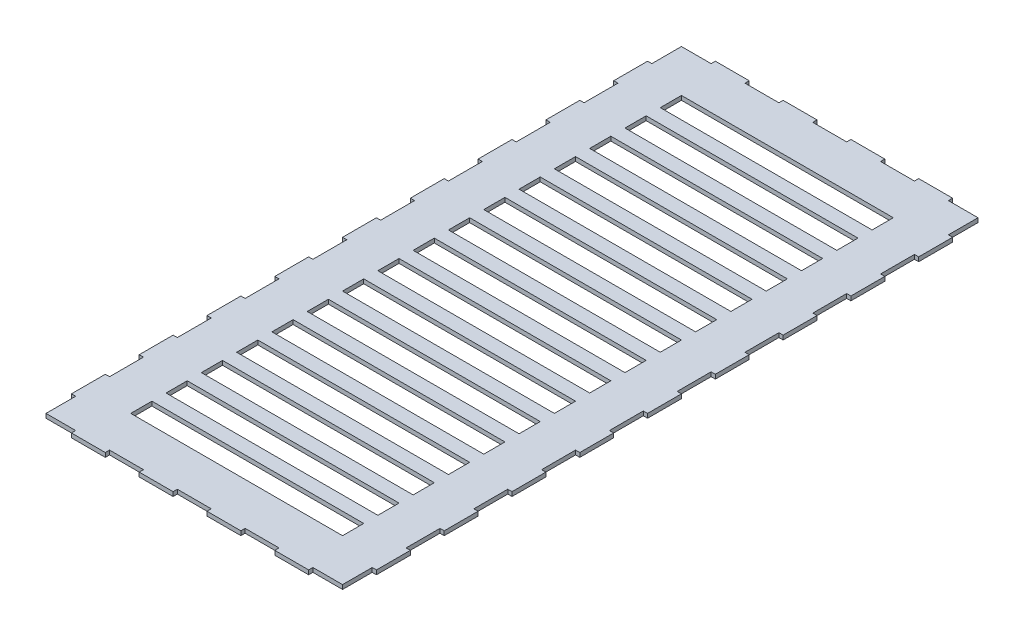
SolidWorks part; units mm, degrees
ref_plane "Front Plane" through (0, 0, 0) normal (0, 0, 1) x (1, 0, 0)
ref_plane "Top Plane" through (0, 0, 0) normal (0, 1, 0) x (1, 0, 0)
ref_plane "Right Plane" through (0, 0, 0) normal (1, 0, 0) x (0, 0, -1)
sketch "Sketch1" plane through (0, 0, 0) normal (0, 1, 0) x (1, 0, 0)
  line L0 (-75, -170) -> (-75, -155)
  line L1 (-105, -225) -> (105, -225)
  line L2 (-105, -225) -> (-105, 225)
  line L3 (-105, 225) -> (105, 225)
  line L4 (105, -225) -> (105, 225)
  line L5 (-105, -225) -> (105, 225) construction
  line L6 (-105, 225) -> (105, -225) construction
  line L7 (-75, -195) -> (75, -195)
  line L8 (-75, -195) -> (-75, -180)
  line L9 (-75, -180) -> (75, -180)
  line L10 (75, -195) -> (75, -180)
  line L11 (-75, -170) -> (75, -170)
  line L12 (75, -170) -> (75, -155)
  line L13 (-75, -155) -> (75, -155)
  line L14 (-75, -145) -> (-75, -130)
  line L15 (-75, -145) -> (75, -145)
  line L16 (75, -145) -> (75, -130)
  line L17 (-75, -130) -> (75, -130)
  line L18 (-75, -120) -> (-75, -105)
  line L19 (-75, -120) -> (75, -120)
  line L20 (75, -120) -> (75, -105)
  line L21 (-75, -105) -> (75, -105)
  line L22 (-75, -95) -> (-75, -80)
  line L23 (-75, -95) -> (75, -95)
  line L24 (75, -95) -> (75, -80)
  line L25 (-75, -80) -> (75, -80)
  line L26 (-75, -70) -> (-75, -55)
  line L27 (-75, -70) -> (75, -70)
  line L28 (75, -70) -> (75, -55)
  line L29 (-75, -55) -> (75, -55)
  line L30 (-75, -45) -> (-75, -30)
  line L31 (-75, -45) -> (75, -45)
  line L32 (75, -45) -> (75, -30)
  line L33 (-75, -30) -> (75, -30)
  line L34 (-75, -20) -> (-75, -5)
  line L35 (-75, -20) -> (75, -20)
  line L36 (75, -20) -> (75, -5)
  line L37 (-75, -5) -> (75, -5)
  line L38 (-75, 5) -> (-75, 20)
  line L39 (-75, 5) -> (75, 5)
  line L40 (75, 5) -> (75, 20)
  line L41 (-75, 20) -> (75, 20)
  line L42 (-75, 30) -> (-75, 45)
  line L43 (-75, 30) -> (75, 30)
  line L44 (75, 30) -> (75, 45)
  line L45 (-75, 45) -> (75, 45)
  line L46 (-75, 55) -> (-75, 70)
  line L47 (-75, 55) -> (75, 55)
  line L48 (75, 55) -> (75, 70)
  line L49 (-75, 70) -> (75, 70)
  line L50 (-75, 80) -> (-75, 95)
  line L51 (-75, 80) -> (75, 80)
  line L52 (75, 80) -> (75, 95)
  line L53 (-75, 95) -> (75, 95)
  line L54 (-75, 105) -> (-75, 120)
  line L55 (-75, 105) -> (75, 105)
  line L56 (75, 105) -> (75, 120)
  line L57 (-75, 120) -> (75, 120)
  line L58 (-75, 130) -> (-75, 145)
  line L59 (-75, 130) -> (75, 130)
  line L60 (75, 130) -> (75, 145)
  line L61 (-75, 145) -> (75, 145)
  line L62 (-75, 155) -> (-75, 170)
  line L63 (-75, 155) -> (75, 155)
  line L64 (75, 155) -> (75, 170)
  line L65 (-75, 170) -> (75, 170)
  line L66 (-75, 180) -> (-75, 195)
  line L67 (-75, 180) -> (75, 180)
  line L68 (75, 180) -> (75, 195)
  line L69 (-75, 195) -> (75, 195)
  point P0 (0, 0)
  dimension "D1" = 30
  dimension "D2" = 30
  dimension "D3" = 30
  dimension "D4" = 15
  dimension "D5" = 150
  dimension "D7" = 30
  dimension "D8" = 10
  dimension "D6" = 16
extrude "Boss-Extrude1" add sketch "Sketch1" along normal blind 3
sketch "Sketch2" plane through (0, 3, 0) normal (0, 1, 0) x (1, 0, 0)
  line L0 (105, 225) -> (-105, 225) construction
  line L1 (-84, 225) -> (-60, 225)
  line L2 (-84, 225) -> (-84, 228)
  line L3 (-84, 228) -> (-60, 228)
  line L4 (-60, 225) -> (-60, 228)
  line L5 (-36, 225) -> (-36, 228)
  line L6 (-36, 225) -> (-12, 225)
  line L7 (-12, 225) -> (-12, 228)
  line L8 (-36, 228) -> (-12, 228)
  line L9 (12, 225) -> (12, 228)
  line L10 (12, 225) -> (36, 225)
  line L11 (36, 225) -> (36, 228)
  line L12 (12, 228) -> (36, 228)
  line L13 (60, 225) -> (60, 228)
  line L14 (60, 225) -> (84, 225)
  line L15 (84, 225) -> (84, 228)
  line L16 (60, 228) -> (84, 228)
  line L17 (-36, -228) -> (-36, -225)
  line L18 (-36, -228) -> (-12, -228)
  line L19 (-12, -228) -> (-12, -225)
  line L20 (-36, -225) -> (-12, -225)
  line L21 (12, -228) -> (12, -225)
  line L22 (12, -228) -> (36, -228)
  line L23 (36, -228) -> (36, -225)
  line L24 (12, -225) -> (36, -225)
  line L25 (60, -228) -> (60, -225)
  line L26 (60, -228) -> (84, -228)
  line L27 (84, -228) -> (84, -225)
  line L28 (60, -225) -> (84, -225)
  line L29 (-84, -228) -> (-84, -225)
  line L30 (-84, -228) -> (-60, -228)
  line L31 (-60, -228) -> (-60, -225)
  line L32 (-84, -225) -> (-60, -225)
  line L33 (-84, 225) -> (-84, -228) construction
  line L34 (-12, 225) -> (12, 225)
  line L35 (-12, -225) -> (12, -225)
  line L38 (105, -225) -> (105, 225) construction
  point P6 (0, 225)
  point P7 (-72, 225)
  point P8 (0, -225)
  dimension "D1" = 3
  dimension "D2" = 24
  dimension "D5" = 453
  dimension "D6" = 24
  dimension "D7" = 450
  dimension "D3" = 4
  dimension "D4" = 2
sketch "Sketch3" plane through (0, 3, 0) normal (0, 1, 0) x (1, 0, 0)
  line L0 (-105, 225) -> (-105, -225) construction
  line L1 (-105, 204) -> (-108, 204)
  line L2 (-105, 204) -> (-105, 180)
  line L3 (-105, 180) -> (-108, 180)
  line L4 (-108, 204) -> (-108, 180)
  line L5 (108, 204) -> (108, 180)
  line L6 (108, 204) -> (105, 204)
  line L7 (105, 204) -> (105, 180)
  line L8 (108, 180) -> (105, 180)
  line L9 (108, 156) -> (108, 132)
  line L10 (108, 156) -> (105, 156)
  line L11 (105, 156) -> (105, 132)
  line L12 (108, 132) -> (105, 132)
  line L13 (108, 108) -> (108, 84)
  line L14 (108, 108) -> (105, 108)
  line L15 (105, 108) -> (105, 84)
  line L16 (108, 84) -> (105, 84)
  line L17 (108, 60) -> (108, 36)
  line L18 (108, 60) -> (105, 60)
  line L19 (105, 60) -> (105, 36)
  line L20 (108, 36) -> (105, 36)
  line L21 (108, 12) -> (108, -12)
  line L22 (108, 12) -> (105, 12)
  line L23 (105, 12) -> (105, -12)
  line L24 (108, -12) -> (105, -12)
  line L25 (108, -36) -> (108, -60)
  line L26 (108, -36) -> (105, -36)
  line L27 (105, -36) -> (105, -60)
  line L28 (108, -60) -> (105, -60)
  line L29 (108, -84) -> (108, -108)
  line L30 (108, -84) -> (105, -84)
  line L31 (105, -84) -> (105, -108)
  line L32 (108, -108) -> (105, -108)
  line L33 (108, -132) -> (108, -156)
  line L34 (108, -132) -> (105, -132)
  line L35 (105, -132) -> (105, -156)
  line L36 (108, -156) -> (105, -156)
  line L37 (108, -180) -> (108, -204)
  line L38 (108, -180) -> (105, -180)
  line L39 (105, -180) -> (105, -204)
  line L40 (108, -204) -> (105, -204)
  line L41 (-105, 156) -> (-105, 132)
  line L42 (-105, 156) -> (-108, 156)
  line L43 (-108, 156) -> (-108, 132)
  line L44 (-105, 132) -> (-108, 132)
  line L45 (-105, 108) -> (-105, 84)
  line L46 (-105, 108) -> (-108, 108)
  line L47 (-108, 108) -> (-108, 84)
  line L48 (-105, 84) -> (-108, 84)
  line L49 (-105, 60) -> (-105, 36)
  line L50 (-105, 60) -> (-108, 60)
  line L51 (-108, 60) -> (-108, 36)
  line L52 (-105, 36) -> (-108, 36)
  line L53 (-105, 12) -> (-105, -12)
  line L54 (-105, 12) -> (-108, 12)
  line L55 (-108, 12) -> (-108, -12)
  line L56 (-105, -12) -> (-108, -12)
  line L57 (-105, -36) -> (-105, -60)
  line L58 (-105, -36) -> (-108, -36)
  line L59 (-108, -36) -> (-108, -60)
  line L60 (-105, -60) -> (-108, -60)
  line L61 (-105, -84) -> (-105, -108)
  line L62 (-105, -84) -> (-108, -84)
  line L63 (-108, -84) -> (-108, -108)
  line L64 (-105, -108) -> (-108, -108)
  line L65 (-105, -132) -> (-105, -156)
  line L66 (-105, -132) -> (-108, -132)
  line L67 (-108, -132) -> (-108, -156)
  line L68 (-105, -156) -> (-108, -156)
  line L69 (-105, -180) -> (-105, -204)
  line L70 (-105, -180) -> (-108, -180)
  line L71 (-108, -180) -> (-108, -204)
  line L72 (-105, -204) -> (-108, -204)
  line L73 (-105, 204) -> (108, 204) construction
  line L74 (-105, 204) -> (-105, 156) construction
  point P7 (-105, 0)
  dimension "D1" = 3
  dimension "D2" = 24
  dimension "D5" = 213
  dimension "D6" = 48
  dimension "D3" = 2
  dimension "D4" = 9
extrude "Boss-Extrude3" add sketch "Sketch3" against normal blind 3
extrude "Boss-Extrude4" add sketch "Sketch2" against normal blind 3 contours L1 L4 L3 L2 | L8 L5 L6 L7 | L12 L9 L10 L11 | L16 L13 L14 L15 | L32 L29 L30 L31 | L20 L17 L18 L19 | L24 L21 L22 L23 | L28 L27 L26 L25
